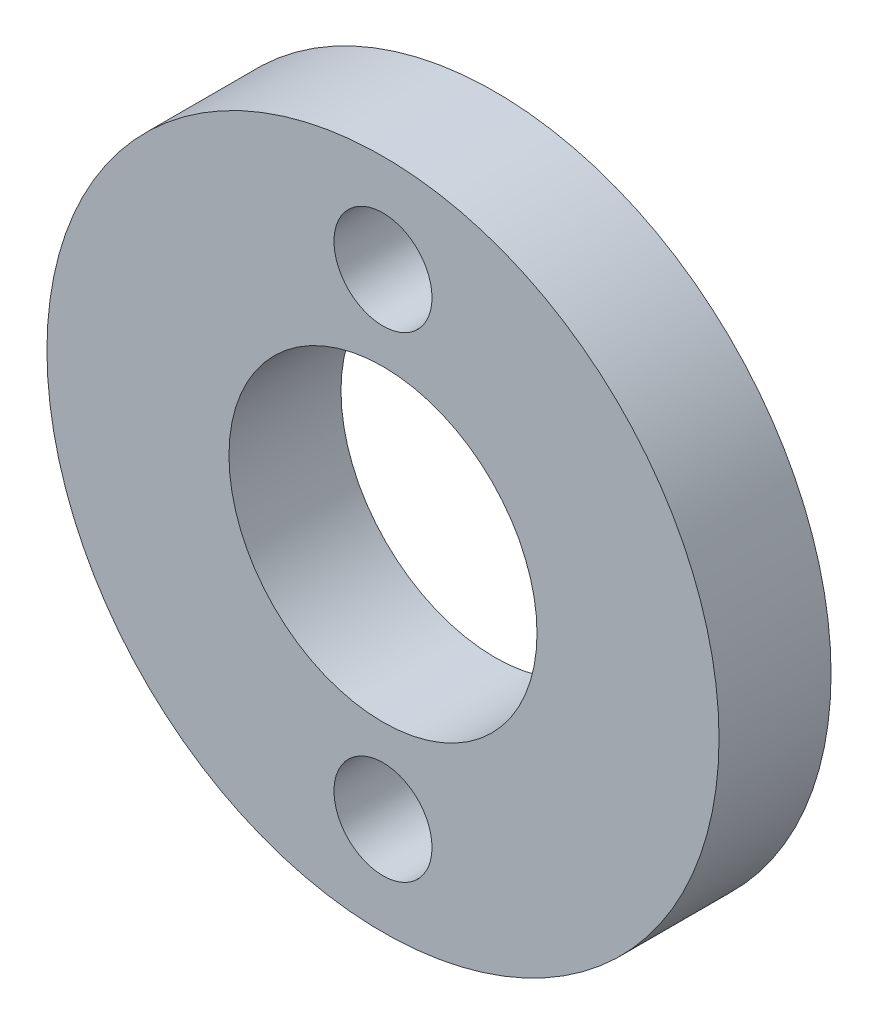
SolidWorks part; units mm, degrees
ref_plane "Спереди" through (0, 0, 0) normal (0, 0, 1) x (1, 0, 0)
ref_plane "Сверху" through (0, 0, 0) normal (0, 1, 0) x (1, 0, 0)
ref_plane "Справа" through (0, 0, 0) normal (1, 0, 0) x (0, 0, -1)
sketch "Эскиз1" plane through (0, 0, 0) normal (0, 0, 1) x (1, 0, 0)
  line L0 (0, 8.5) -> (0, -8.5) construction
  circle A0 centre (0, 0) radius 12
  circle A1 centre (0, 0) radius 5.5
  circle A2 centre (0, 8.5) radius 1.75
  circle A3 centre (0, -8.5) radius 1.75
  dimension "D1" = 24
  dimension "D2" = 11
  dimension "D3" = 17
  dimension "D4" = 3.5
extrude "Бобышка-Вытянуть1" add sketch "Эскиз1" along normal blind 4
